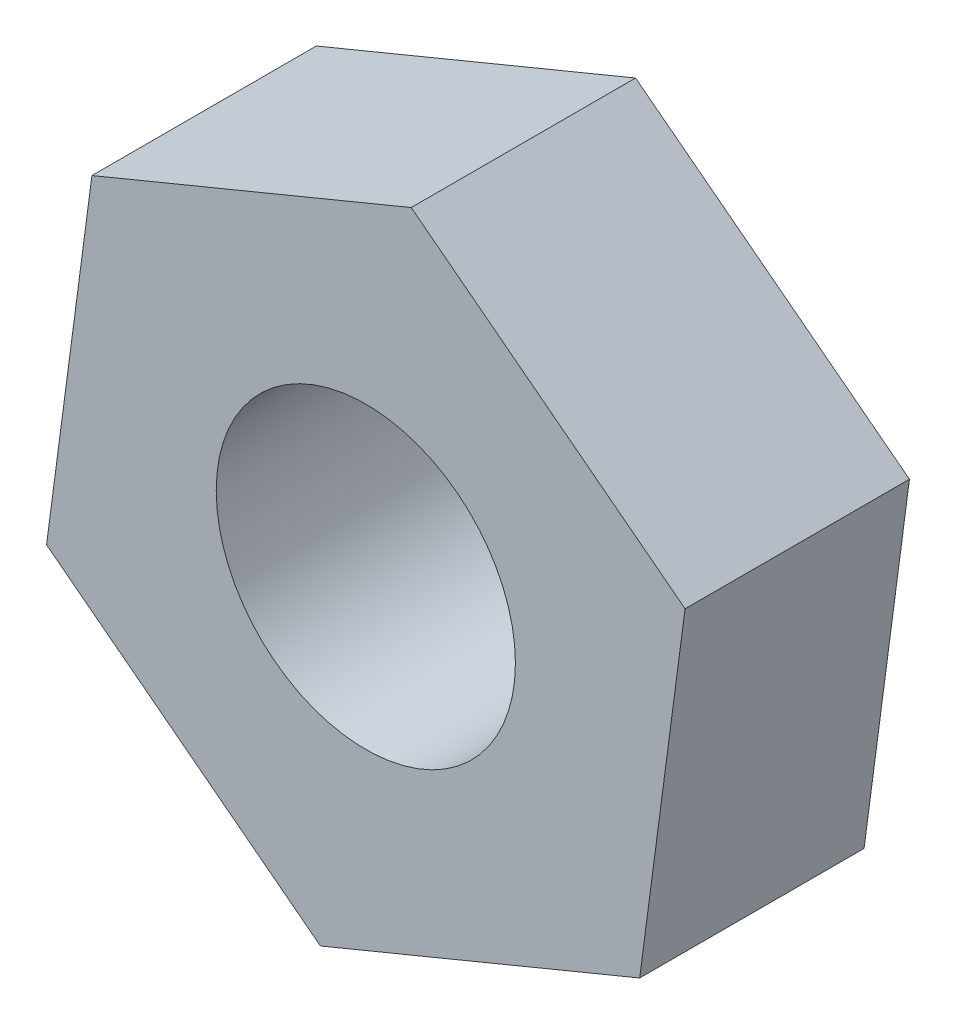
SolidWorks part; units mm, degrees
ref_plane "前视基准面" through (0, 0, 0) normal (0, 0, 1) x (1, 0, 0)
ref_plane "上视基准面" through (0, 0, 0) normal (0, 1, 0) x (1, 0, 0)
ref_plane "右视基准面" through (0, 0, 0) normal (1, 0, 0) x (0, 0, -1)
sketch "草图1" plane through (0, 0, 0) normal (0, 0, 1) x (1, 0, 0)
  line L1 (1.8309, -1.4075) -> (2.1344, 0.8819)
  line L2 (2.1344, 0.8819) -> (0.3034, 2.2894)
  line L3 (0.3034, 2.2894) -> (-1.8309, 1.4075)
  line L4 (-1.8309, 1.4075) -> (-2.1344, -0.8819)
  line L5 (-2.1344, -0.8819) -> (-0.3034, -2.2894)
  line L6 (-0.3034, -2.2894) -> (1.8309, -1.4075)
  circle A0 centre (0, 0) radius 2 construction
  circle A1 centre (0, 0) radius 1
  dimension "D2" = 2
  dimension "D1" = 4
extrude "凸台-拉伸1" add sketch "草图1" along normal blind 1.5
